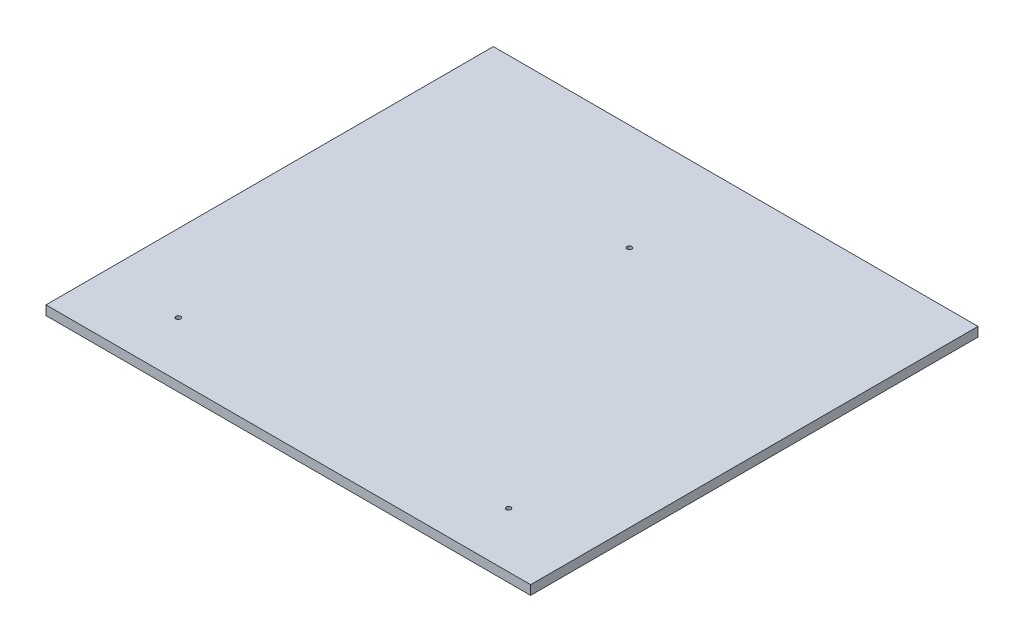
SolidWorks part; units mm, degrees
material "Cedar"
ref_plane "Front Plane" through (0, 0, 0) normal (0, 0, 1) x (1, 0, 0)
ref_plane "Top Plane" through (0, 0, 0) normal (0, 1, 0) x (1, 0, 0)
ref_plane "Right Plane" through (0, 0, 0) normal (1, 0, 0) x (0, 0, -1)
sketch "Sketch1" plane through (0, 0, 0) normal (0, 1, 0) x (1, 0, 0)
  line L1 (0, 0) -> (660.4, 0)
  line L2 (0, 0) -> (0, 609.6)
  line L3 (0, 609.6) -> (660.4, 609.6)
  line L4 (660.4, 0) -> (660.4, 609.6)
  dimension "D1" = 660.4
  dimension "D2" = 609.6
extrude "Boss-Extrude1" add sketch "Sketch1" along normal blind 12.7
sketch "Sketch5" plane through (0, 12.7, 0) normal (0, 1, 0) x (1, 0, 0)
  line L0 (330.2, 609.6) -> (330.2, 464.8281) construction
  line L1 (660.4, 609.6) -> (0, 609.6) construction
  line L2 (0, 0) -> (105.2, 75.1166) construction
  line L3 (660.4, 0) -> (555.2, 75.1166) construction
  line L5 (330.2, 464.8281) -> (105.2, 75.1166) construction
  line L6 (105.2, 75.1166) -> (555.2, 75.1166) construction
  line L7 (555.2, 75.1166) -> (330.2, 464.8281) construction
  line L8 (330.2, 464.8281) -> (330.2, 75.1166) construction
  circle A0 centre (105.2, 75.1166) radius 3.175
  circle A1 centre (555.2, 75.1166) radius 3.175
  circle A2 centre (330.2, 464.8281) radius 3.175
  dimension "D6" = 6.35
  dimension "D7" = 6.35
  dimension "D8" = 6.35
  dimension "D1" = 450
extrude "Cut-Extrude2" cut sketch "Sketch5" against normal through all
sketch "Sketch6" plane through (0, 12.7, 0) normal (0, 1, 0) x (1, 0, 0)
  line L0 (0, 609.6) -> (660.4, 0) construction
  line L1 (660.4, 609.6) -> (0, 0) construction
  point P8 (330.2, 304.8)
sketch "Sketch7" plane through (0, 12.7, 0) normal (0, 1, 0) x (1, 0, 0)
  circle A0 centre (17.9605, 17.9605) radius 17
